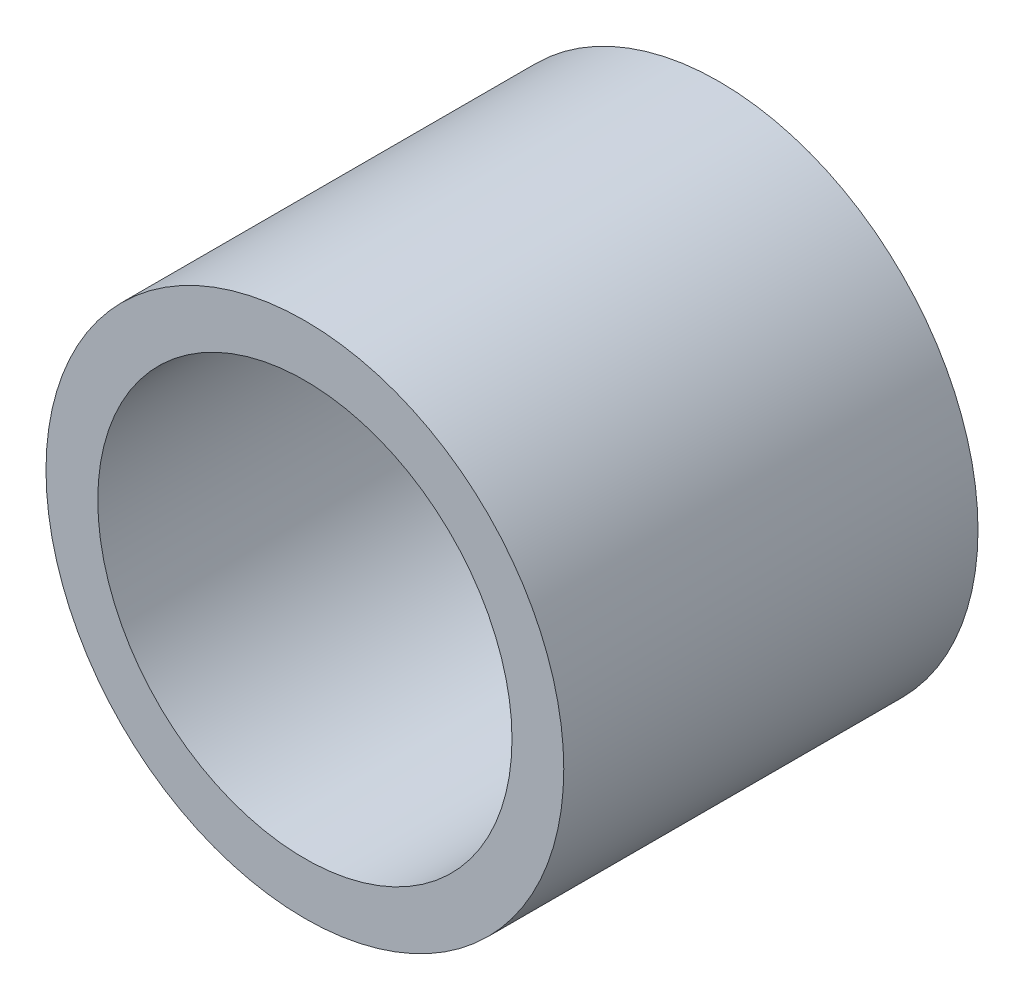
SolidWorks part; units mm, degrees
material "Nylon 101"
ref_plane "Front Plane" through (0, 0, 0) normal (0, 0, 1) x (1, 0, 0)
ref_plane "Top Plane" through (0, 0, 0) normal (0, 1, 0) x (1, 0, 0)
ref_plane "Right Plane" through (0, 0, 0) normal (1, 0, 0) x (0, 0, -1)
sketch "Sketch1" plane through (0, 0, 0) normal (0, 0, 1) x (1, 0, 0)
  circle A0 centre (0, 0) radius 7.9375
  circle A1 centre (0, 0) radius 6.35
  dimension "D1" = 15.875
  dimension "ID" = 12.7
extrude "Extrude1" add sketch "Sketch1" along normal mid plane 12.7
sketch "Sketch2" plane through (0, 0, 0) normal (1, 0, 0) x (0, 0, -1)
  line L0 (-6.35, -6.35) -> (6.35, -6.35) construction
  line L3 (6.35, 6.35) -> (-6.35, 6.35) construction
  line L5 (-6.35, -6.35) -> (6.35, -6.35)
  line L6 (6.35, 6.35) -> (-6.35, 6.35)
sketch "Sketch4" plane through (0, 0, 6.35) normal (0, 0, 1) x (1, 0, 0)
  line L0 (0, 0) -> (-4.4901, 4.4901)
  line L1 (0, -3.4925) -> (0, 3.4925) construction
  circle A0 centre (0, 0) radius 6.35 construction
  dimension "D1" = 45
